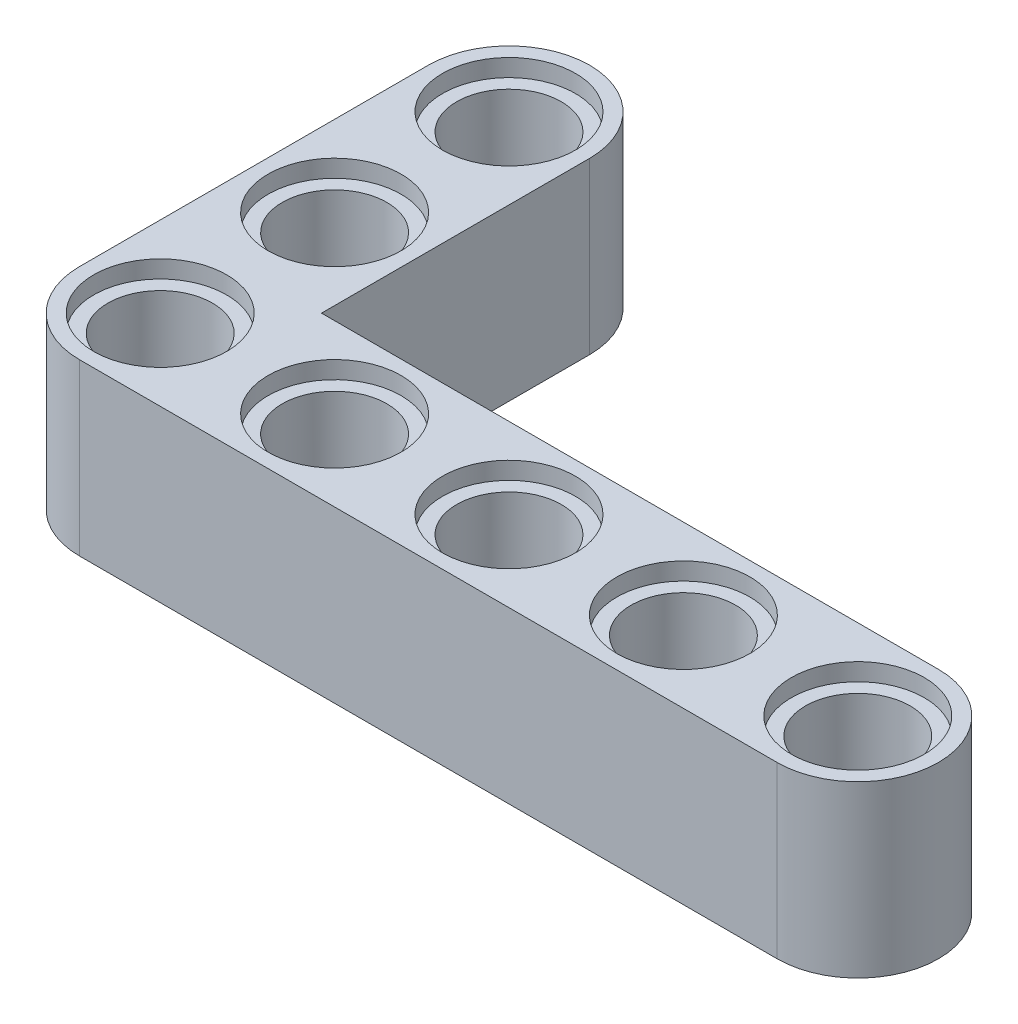
SolidWorks part; units mm, degrees
ref_plane "Front Plane" through (0, 0, 0) normal (0, 0, 1) x (1, 0, 0)
ref_plane "Top Plane" through (0, 0, 0) normal (0, 1, 0) x (1, 0, 0)
ref_plane "Right Plane" through (0, 0, 0) normal (1, 0, 0) x (0, 0, -1)
sketch "Sketch1" plane through (0, 0, 0) normal (0, 1, 0) x (1, 0, 0)
  line L1 (-12.3, 3.7) -> (16, 3.7)
  line L9 (-12.3, 3.7) -> (-12.3, 16)
  line L11 (-19.7, 16) -> (-19.7, 0)
  line L12 (-16, -3.7) -> (16, -3.7)
  arc A9 (16, 3.7) -> (16, -3.7) centre (16, 0) cw
  arc A10 (-19.7, 0) -> (-16, -3.7) centre (-16, 0) ccw
  arc A12 (-12.3, 16) -> (-19.7, 16) centre (-16, 16) ccw
  point P20 (8, -3.7)
  point P25 (-8, -3.7)
  dimension "D1" = 16
  dimension "D3" = 3.7
  dimension "D4" = 3.7
  dimension "D5" = 3.7
  dimension "D2" = 32
  dimension "D6" = 12.3
extrude "Boss-Extrude3" add sketch "Sketch1" along normal blind 7.8 contours A10 L12 A9 L1 L9 A12 L11
sketch "Sketch2" plane through (0, 7.8, 0) normal (0, 1, 0) x (1, 0, 0)
  circle A0 centre (0, 0) radius 2.4
  circle A2 centre (8, 0) radius 2.4
  circle A5 centre (16, 0) radius 2.4
  circle A6 centre (-16, 0) radius 2.4
  circle A9 centre (-8, 0) radius 2.4
  circle A10 centre (-16, 16) radius 2.4
  circle A11 centre (-16, 8) radius 2.4
  dimension "D1" = 4.8
  dimension "D2" = 8
sketch "Sketch3" plane through (0, 7.8, 0) normal (0, 1, 0) x (1, 0, 0)
  circle A0 centre (0, 0) radius 3.05
  circle A1 centre (8, 0) radius 3.05
  circle A2 centre (16, 0) radius 3.05
  circle A3 centre (-16, 0) radius 3.05
  circle A4 centre (-8, 0) radius 3.05
  circle A5 centre (-16, 8) radius 3.05
  circle A6 centre (-16, 16) radius 3.05
  dimension "D1" = 8
  dimension "D2" = 6.1
sketch "Sketch4" plane through (0, 0, 0) normal (0, -1, 0) x (1, 0, 0)
  circle A0 centre (0, 0) radius 3.05
  circle A1 centre (8, 0) radius 3.05
  circle A2 centre (16, 0) radius 3.05
  circle A3 centre (-16, 0) radius 3.05
  circle A4 centre (-8, 0) radius 3.05
  circle A5 centre (-16, -8) radius 3.05
  circle A6 centre (-16, -16) radius 3.05
  dimension "D1" = 6.1
  dimension "D2" = 8
extrude "Cut-Extrude9" cut sketch "Sketch2" against normal blind 7.8
extrude "Cut-Extrude10" cut sketch "Sketch3" against normal blind 0.8
extrude "Cut-Extrude11" cut sketch "Sketch4" against normal blind 0.8
